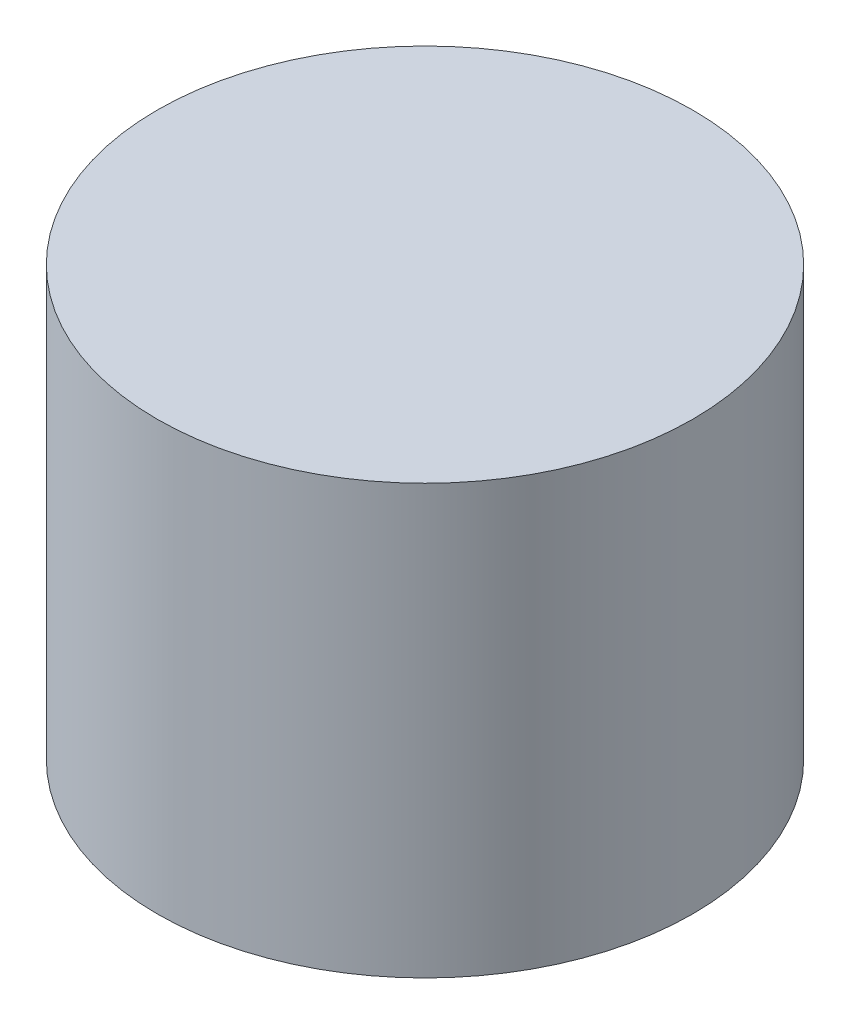
SolidWorks part; units mm, degrees
material "Silicon"
ref_plane "Front Plane" through (0, 0, 0) normal (0, 0, 1) x (1, 0, 0)
ref_plane "Top Plane" through (0, 0, 0) normal (0, 1, 0) x (1, 0, 0)
ref_plane "Right Plane" through (0, 0, 0) normal (1, 0, 0) x (0, 0, -1)
sketch "Shock Cord Bundle Profile" plane through (0, 0, 0) normal (0, 1, 0) x (1, 0, 0)
  circle A0 centre (0, 0) radius 63.5
  dimension "D1" = 127
extrude "Shock Cord Bundle Body" add sketch "Shock Cord Bundle Profile" along normal blind 101.6
equation "\"Packed Length\"= 4"
equation "\"Packed Diameter\"= 5"
equation "\"D1@Shock Cord Bundle Profile\"=\"Packed Diameter\""
equation "\"D1@Shock Cord Bundle Body\"=\"Packed Length\""
